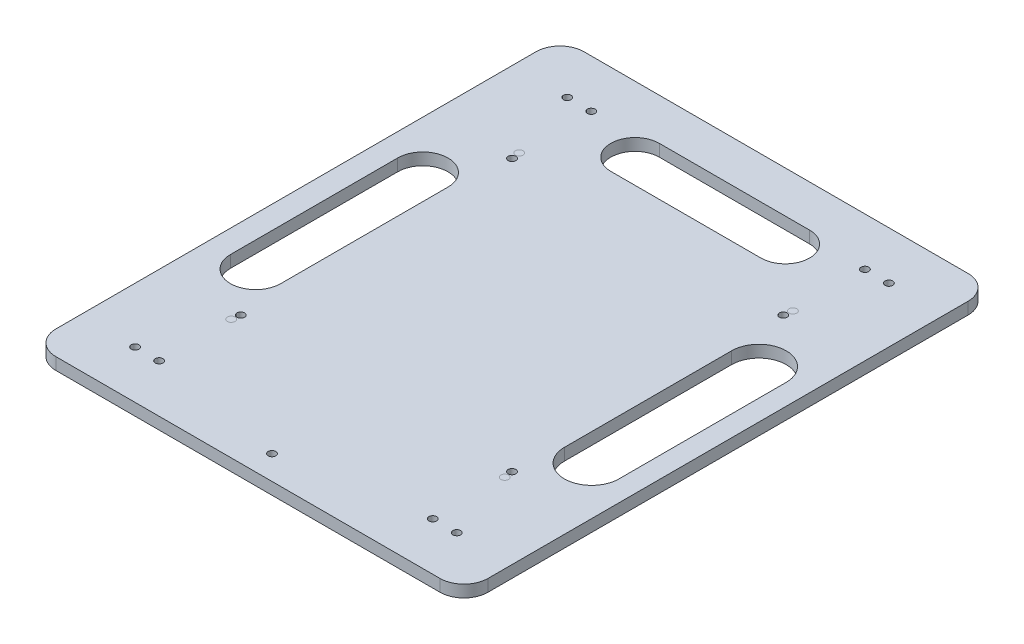
SolidWorks part; units mm, degrees
ref_plane "前视基准面" through (0, 0, 0) normal (0, 0, 1) x (1, 0, 0)
ref_plane "上视基准面" through (0, 0, 0) normal (0, 1, 0) x (1, 0, 0)
ref_plane "右视基准面" through (0, 0, 0) normal (1, 0, 0) x (0, 0, -1)
sketch "草图1" plane through (0, 0, 0) normal (0, 1, 0) x (1, 0, 0)
  line L0 (-114.0741, 75.3411) -> (-81.0741, 75.3411) construction
  line L1 (-104.0741, 85.3411) -> (55.9259, 85.3411)
  line L2 (-114.0741, 75.3411) -> (-114.0741, -124.6589)
  line L3 (-104.0741, -134.6589) -> (55.9259, -134.6589)
  line L4 (65.9259, 75.3411) -> (65.9259, -124.6589)
  line L5 (65.9259, 75.3411) -> (32.9259, 75.3411) construction
  line L6 (-114.0741, -124.6589) -> (-81.0741, -124.6589) construction
  line L7 (65.9259, -124.6589) -> (32.9259, -124.6589) construction
  line L8 (-81.0741, 85.3411) -> (-81.0741, 35.3411) construction
  line L9 (-81.0741, -134.6589) -> (-81.0741, -84.6589) construction
  line L10 (-81.0741, 35.3411) -> (32.9259, 35.3411) construction
  line L11 (32.9259, 35.3411) -> (32.9259, -84.6589) construction
  arc A0 (-104.0741, 85.3411) -> (-114.0741, 75.3411) centre (-104.0741, 75.3411) ccw
  arc A1 (55.9259, 85.3411) -> (65.9259, 75.3411) centre (55.9259, 75.3411) cw
  arc A2 (55.9259, -134.6589) -> (65.9259, -124.6589) centre (55.9259, -124.6589) ccw
  arc A3 (-114.0741, -124.6589) -> (-104.0741, -134.6589) centre (-104.0741, -124.6589) ccw
  circle A4 centre (-81.0741, 35.3411) radius 1.6
  circle A5 centre (32.9259, 35.3411) radius 1.6
  circle A6 centre (32.9259, -84.6589) radius 1.6
  circle A7 centre (-81.0741, -84.6589) radius 1.6
  point P6 (-114.0741, 85.3411)
  point P9 (65.9259, 85.3411)
  point P14 (-114.0741, -134.6589)
  dimension "D3" = 10
  dimension "D4" = 10
  dimension "D5" = 10
  dimension "D6" = 10
  dimension "D1" = 220
  dimension "D2" = 180
  dimension "D7" = 33
extrude "凸台-拉伸1" add sketch "草图1" along normal blind 5
sketch "草图4" plane through (0, 5, 0) normal (0, 1, 0) x (1, 0, 0)
  line L0 (-24.0741, 85.3411) -> (-24.0741, 75.3411) construction
  line L1 (55.9259, 85.3411) -> (-104.0741, 85.3411) construction
  line L2 (-24.0741, 85.3411) -> (-24.0741, -134.6589) construction
  line L3 (-104.0741, -134.6589) -> (55.9259, -134.6589) construction
  line L4 (65.9259, -24.6589) -> (-114.0741, -24.6589) construction
  line L5 (65.9259, -124.6589) -> (65.9259, 75.3411) construction
  line L6 (-114.0741, 75.3411) -> (-114.0741, -124.6589) construction
  line L7 (-24.0741, -24.6589) -> (32.6259, -24.6589) construction
  line L8 (-24.0741, -24.6589) -> (-80.7741, -24.6589) construction
  line L9 (-24.0741, -24.6589) -> (-24.0741, 31.8411) construction
  line L10 (-24.0741, 31.8411) -> (32.6259, 31.8411) construction
  line L11 (32.6259, 31.8411) -> (32.6259, -24.6589) construction
  line L12 (-24.0741, -24.6589) -> (-24.0741, -81.1589) construction
  line L13 (-24.0741, -81.1589) -> (32.6259, -81.1589) construction
  line L14 (32.6259, -81.1589) -> (32.6259, -24.6589) construction
  line L15 (32.6259, -24.6589) -> (-80.7741, -24.6589) construction
  line L16 (-80.7741, -24.6589) -> (-80.7741, -81.1589) construction
  line L17 (-80.7741, -81.1589) -> (-24.0741, -81.1589) construction
  line L18 (-80.7741, -24.6589) -> (-80.7741, 31.8411) construction
  line L19 (-80.7741, 31.8411) -> (-24.0741, 31.8411) construction
  line L20 (-81.0741, 35.3411) -> (-81.0741, 65.3411) construction
  line L21 (32.9259, 35.3411) -> (32.9259, 65.3411)
  line L22 (-81.0741, -84.6589) -> (-81.0741, -114.6589) construction
  line L23 (32.9259, -84.6589) -> (32.9259, -114.6589) construction
  circle A0 centre (-24.0741, 75.3411) radius 1.6
  circle A1 centre (-81.0741, 65.3411) radius 1.6
  circle A2 centre (32.9259, 65.3411) radius 1.6
  circle A3 centre (-81.0741, -114.6589) radius 1.6
  circle A4 centre (32.9259, -114.6589) radius 1.6
  circle A5 centre (-81.0741, 35.3411) radius 1.6
  circle A6 centre (32.9259, 35.3411) radius 1.6
  circle A7 centre (32.9259, -84.6589) radius 1.6
  circle A8 centre (-81.0741, -84.6589) radius 1.6
  circle A9 centre (-80.7741, 31.8411) radius 1.6
  circle A10 centre (32.6259, 31.8411) radius 1.6
  circle A11 centre (32.6259, -81.1589) radius 1.6
  circle A12 centre (-80.7741, -81.1589) radius 1.6
  dimension "D1" = 3.2
  dimension "D2" = 56.7
extrude "切除-拉伸2" cut sketch "草图4" against normal blind 10 contours A3 | A4 | A2 | A1
sketch "草图5" plane through (0, 5, 0) normal (0, 1, 0) x (1, 0, 0)
  circle A0 centre (-81.0741, 35.3411) radius 1.6
  circle A1 centre (32.9259, 35.3411) radius 1.6
  circle A2 centre (32.9259, -84.6589) radius 1.6
  circle A3 centre (-81.0741, -84.6589) radius 1.6
extrude "凸台-拉伸3" add sketch "草图5" against normal blind 5 separate body
sketch "草图6" plane through (0, 5, 0) normal (0, 1, 0) x (1, 0, 0)
  line L0 (-24.0741, 85.3411) -> (-24.0741, -134.6589) construction
  line L1 (55.9259, 85.3411) -> (-104.0741, 85.3411) construction
  line L2 (-104.0741, -134.6589) -> (55.9259, -134.6589) construction
  line L3 (-24.0741, -134.6589) -> (-114.0741, -24.6589) construction
  line L4 (-114.0741, 75.3411) -> (-114.0741, -124.6589) construction
  line L5 (-114.0741, -24.6589) -> (65.9259, -24.6589) construction
  line L6 (65.9259, -124.6589) -> (65.9259, 75.3411) construction
  line L7 (-24.0741, -24.6589) -> (32.4259, -24.6589) construction
  line L8 (-24.0741, -24.6589) -> (-80.5741, -24.6589) construction
  line L9 (-24.0741, -24.6589) -> (-24.0741, 31.8411) construction
  line L10 (-24.0741, -24.6589) -> (-24.0741, -81.1589) construction
  line L11 (-24.0741, 31.8411) -> (32.4259, 31.8411) construction
  line L12 (32.4259, 31.8411) -> (32.4259, -24.6589) construction
  line L13 (-24.0741, -81.1589) -> (-80.5741, -81.1589) construction
  line L14 (-80.5741, -81.1589) -> (-80.5741, -24.6589) construction
  line L15 (-24.0741, -81.1589) -> (32.4259, -81.1589) construction
  line L16 (32.4259, -81.1589) -> (32.4259, -24.6589) construction
  line L17 (-24.0741, 31.8411) -> (-80.5741, 31.8411) construction
  line L18 (-80.5741, 31.8411) -> (-80.5741, -24.6589) construction
  circle A0 centre (-80.5741, -81.1589) radius 1.6
  circle A1 centre (-80.5741, 31.8411) radius 1.6
  circle A2 centre (32.4259, 31.8411) radius 1.6
  circle A3 centre (32.4259, -81.1589) radius 1.6
extrude "切除-拉伸3" cut sketch "草图6" against normal blind 5
sketch "草图8" plane through (0, 0, 0) normal (0, -1, 0) x (1, 0, 0)
  line L0 (-24.0741, 134.6589) -> (-24.0741, 124.6589) construction
  line L1 (-104.0741, 134.6589) -> (55.9259, 134.6589) construction
  circle A0 centre (-24.0741, 124.6589) radius 1.6
extrude "切除-拉伸4" cut sketch "草图8" against normal blind 5
sketch "草图9" plane through (0, 0, 0) normal (0, -1, 0) x (1, 0, 0)
  line L0 (-114.0741, 24.6589) -> (65.9259, 24.6589) construction
  line L1 (-114.0741, -75.3411) -> (-114.0741, 124.6589) construction
  line L2 (65.9259, 124.6589) -> (65.9259, -75.3411) construction
  line L3 (-24.0741, 134.6589) -> (-24.0741, -85.3411) construction
  line L4 (-104.0741, 134.6589) -> (55.9259, 134.6589) construction
  line L5 (55.9259, -85.3411) -> (-104.0741, -85.3411) construction
  line L6 (-114.0741, 24.6589) -> (-94.0741, 24.6589) construction
  line L7 (65.9259, 24.6589) -> (45.9259, 24.6589) construction
  line L8 (-94.0741, 61.4612) -> (-94.0741, -8.2026) construction
  line L9 (-83.5838, 61.4612) -> (-83.5838, -8.2026)
  line L10 (-104.5644, 61.4612) -> (-104.5644, -8.2026)
  line L11 (45.9259, 61.4612) -> (45.9259, -8.2026) construction
  line L12 (57.3035, 61.4612) -> (57.3035, -8.2026)
  line L13 (34.5483, 61.4612) -> (34.5483, -8.2026)
  line L14 (-55.3481, -57.8722) -> (7.2271, -57.8722) construction
  line L15 (-55.3481, -47.7637) -> (7.2271, -47.7637)
  line L16 (-55.3481, -67.9807) -> (7.2271, -67.9807)
  arc A0 (-83.5838, 61.4612) -> (-104.5644, 61.4612) centre (-94.0741, 61.4612) ccw
  arc A1 (-104.5644, -8.2026) -> (-83.5838, -8.2026) centre (-94.0741, -8.2026) ccw
  arc A2 (57.3035, 61.4612) -> (34.5483, 61.4612) centre (45.9259, 61.4612) ccw
  arc A3 (34.5483, -8.2026) -> (57.3035, -8.2026) centre (45.9259, -8.2026) ccw
  arc A4 (-55.3481, -47.7637) -> (-55.3481, -67.9807) centre (-55.3481, -57.8722) ccw
  arc A5 (7.2271, -67.9807) -> (7.2271, -47.7637) centre (7.2271, -57.8722) ccw
  point P16 (-94.0741, 26.6293)
  point P21 (45.9259, 26.6293)
  point P30 (-24.0605, -57.8722)
extrude "切除-拉伸5" cut sketch "草图9" against normal blind 10
sketch "草图10" plane through (0, 5, 0) normal (0, 1, 0) x (1, 0, 0)
  line L0 (-81.0741, 65.3411) -> (-91.0741, 65.3411) construction
  line L1 (32.9259, 65.3411) -> (42.9259, 65.3411) construction
  line L2 (-81.0741, -114.6589) -> (-91.0741, -114.6589) construction
  line L3 (32.9259, -114.6589) -> (42.9259, -114.6589) construction
  circle A0 centre (-91.0741, 65.3411) radius 1.6
  circle A1 centre (42.9259, 65.3411) radius 1.6
  circle A2 centre (-91.0741, -114.6589) radius 1.6
  circle A3 centre (42.9259, -114.6589) radius 1.6
extrude "切除-拉伸6" cut sketch "草图10" against normal blind 10
